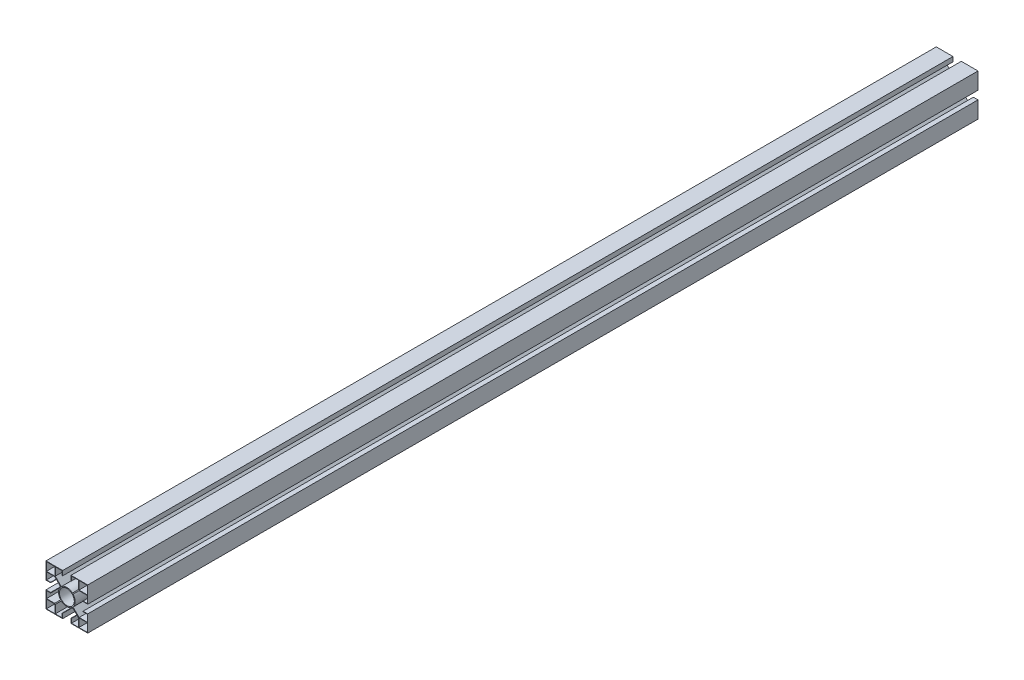
SolidWorks part; units mm, degrees
material "201.0-T7 Molde de fundição com isolamento (SS)"
ref_plane "Plano frontal" through (0, 0, 0) normal (0, 0, 1) x (1, 0, 0)
ref_plane "Plano superior" through (0, 0, 0) normal (0, 1, 0) x (1, 0, 0)
ref_plane "Plano direito" through (0, 0, 0) normal (1, 0, 0) x (0, 0, -1)
sketch "Esboço1" plane through (0, 0, 0) normal (0, 0, 1) x (1, 0, 0)
  line L1 (-6.0006, -6.7077) -> (-12.5, -13.2071)
  line L2 (22.5, -22.5) -> (22.5, -4.5)
  line L3 (22.5, 22.5) -> (4.5, 22.5)
  line L4 (-22.5, -22.5) -> (-22.5, -4.5)
  line L5 (-5, -22) -> (-5, -17.5)
  line L6 (-5, -22) -> (-22, -22)
  line L7 (-22.5, 22.5) -> (-12.5, 22.5)
  line L8 (-22.5, 22.5) -> (-22.5, 12.5)
  line L9 (-22, 12.5) -> (-13.2071, 12.5)
  line L10 (-12.5, 22) -> (-12.5, 13.2071)
  line L11 (22.5, 22.5) -> (12.5, 22.5)
  line L12 (22.5, 22.5) -> (22.5, 12.5)
  line L13 (22.5, 12.5) -> (13.2071, 12.5)
  line L14 (12.5, 22.5) -> (12.5, 13.2071)
  line L15 (-22, -22) -> (-22, -5)
  line L16 (-22, -5) -> (-17.5, -5)
  line L17 (-22, 22) -> (-22, 13)
  line L18 (6.7077, 6.0006) -> (13.2071, 12.5)
  line L19 (6.0006, 6.7077) -> (12.5, 13.2071)
  line L20 (-6.7077, 6.0006) -> (-13.2071, 12.5)
  line L21 (-22, 13) -> (-13, 13)
  line L22 (-17.5, -5) -> (-17.5, -4.5)
  line L23 (-13, 22) -> (-13, 13)
  line L24 (-22.5, 12.5) -> (-12.5, 12.5) construction
  line L25 (-22, 22) -> (-13, 22)
  line L26 (22, 22) -> (13, 22)
  line L27 (13, 22) -> (13, 13)
  line L28 (22, 13) -> (13, 13)
  line L29 (22, 22) -> (22, 13)
  line L30 (-6.0006, 6.7077) -> (-12.5, 13.2071)
  line L31 (-12.5, 22.5) -> (-12.5, 12.5) construction
  line L32 (12.5, 22.5) -> (12.5, 12.5) construction
  line L33 (22.5, 12.5) -> (12.5, 12.5) construction
  line L34 (-6.7077, -6.0006) -> (-13.2071, -12.5)
  line L35 (6.0006, -6.7077) -> (12.5, -13.2071)
  line L36 (6.7077, -6.0006) -> (13.2071, -12.5)
  line L37 (12.5, -22) -> (12.5, -13.2071)
  line L38 (22, -22) -> (13, -22)
  line L39 (13, -22) -> (13, -13)
  line L40 (22, -22) -> (22, -13)
  line L41 (22, -13) -> (13, -13)
  line L42 (22, -12.5) -> (13.2071, -12.5)
  line L43 (-12.5, -22) -> (-12.5, -13.2071)
  line L44 (-13, -22) -> (-13, -13)
  line L45 (-22, -22) -> (-22, -13)
  line L46 (-22, -22) -> (-13, -22)
  line L47 (22.5, -22.5) -> (4.5, -22.5)
  line L48 (-22.5, -12.5) -> (-13.2071, -12.5)
  line L49 (-22, -13) -> (-13, -13)
  line L50 (-4.5, 22.5) -> (-4.5, 17.5)
  line L51 (4.5, 22.5) -> (4.5, 17.5)
  line L52 (-4.5, 22.5) -> (-22.5, 22.5)
  line L53 (-4.5, -22.5) -> (-4.5, -17.5)
  line L54 (4.5, -22.5) -> (4.5, -17.5)
  line L55 (-4.5, -22.5) -> (-22.5, -22.5)
  line L56 (-22.5, 4.5) -> (-17.5, 4.5)
  line L57 (-22.5, -4.5) -> (-17.5, -4.5)
  line L59 (-22.5, 4.5) -> (-22.5, 22.5)
  line L60 (22.5, -4.5) -> (17.5, -4.5)
  line L61 (22.5, 4.5) -> (17.5, 4.5)
  line L62 (22.5, 4.5) -> (22.5, 22.5)
  line L63 (-4.5, -17.5) -> (-5, -17.5)
  line L64 (-5, 22) -> (-5, 17.5)
  line L65 (-5, 22) -> (-22.5, 22)
  line L66 (-22, 5) -> (-22, 22.5)
  line L67 (-22, 5) -> (-17.5, 5)
  line L68 (-5, 17.5) -> (-4.5, 17.5)
  line L69 (-17.5, 4.5) -> (-17.5, 5)
  line L70 (22, -5) -> (17.5, -5)
  line L71 (22, -22) -> (22, -5)
  line L72 (22, -22) -> (5, -22)
  line L73 (5, -22) -> (5, -17.5)
  line L74 (4.5, -17.5) -> (5, -17.5)
  line L75 (17.5, -5) -> (17.5, -4.5)
  line L76 (22.5, 22) -> (5, 22)
  line L77 (5, 22) -> (5, 17.5)
  line L78 (22, 5) -> (17.5, 5)
  line L79 (22, 5) -> (22, 22.5)
  line L80 (4.5, 17.5) -> (5, 17.5)
  line L81 (17.5, 5) -> (17.5, 4.5)
  circle A0 centre (0, 0) radius 8
  arc A1 (6.7077, -6.0006) -> (6.7077, 6.0006) centre (0, 0) ccw
  circle A2 centre (0, 0) radius 9 construction
  arc A3 (6.0006, 6.7077) -> (-6.0006, 6.7077) centre (0, 0) ccw
  arc A4 (-6.7077, 6.0006) -> (-6.7077, -6.0006) centre (0, 0) ccw
  arc A5 (-6.0006, -6.7077) -> (6.0006, -6.7077) centre (0, 0) ccw
  point P0 (0, 0)
  dimension "D9" = 8
  dimension "D1" = 45
  dimension "D2" = 8
  dimension "D3" = 0.5
  dimension "D4" = 0.5
  dimension "D5" = 0.5
  dimension "D10" = 5
  dimension "D11" = 5
  dimension "D12" = 8
  dimension "D13" = 5
  dimension "D14" = 8
  dimension "D15" = 5
  dimension "D6" = 0.5
  dimension "D7" = 0.5
extrude "Ressalto-extrusão4" add sketch "Esboço1" along normal blind 960 contours L1 A5 L35 L37 L72 L39 L41 L71 L42 L36 A1 L18 L13 L79 L28 L27 L76 L14 L19 A3 L30 L10 L65 L23 L21 L66 L9 L20 A4 L34 L48 L15 L49 L44 L6 L43 A0 | L53 L63 L5 L6 L15 L48 L4 L55 | L57 L4 L48 L15 L16 L22 | L78 L81 L61 L62 L13 L79 | L79 L13 L62 L76 L29 | L26 L79 L11 L14 L76 | L79 L76 L12 L3 | L51 L80 L77 L76 L14 L3 | L56 L69 L67 L66 L17 L65 L59 | L64 L68 L50 L52 L66 L25 L65 | L65 L66 L7 L8
